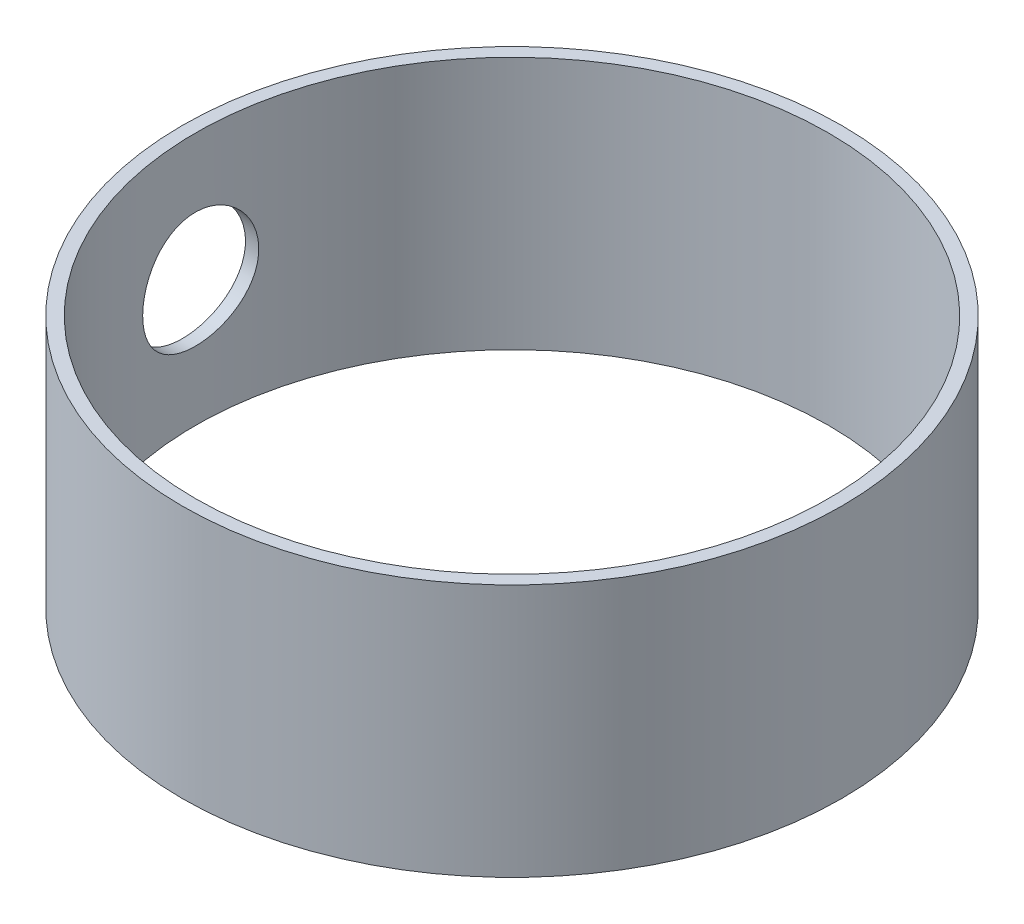
SolidWorks part; units mm, degrees
ref_plane "Front Plane" through (0, 0, 0) normal (0, 0, 1) x (1, 0, 0)
ref_plane "Top Plane" through (0, 0, 0) normal (0, 1, 0) x (1, 0, 0)
ref_plane "Right Plane" through (0, 0, 0) normal (1, 0, 0) x (0, 0, -1)
sketch "Sketch1" plane through (0, 0, 0) normal (0, 1, 0) x (1, 0, 0)
  circle A0 centre (0, 0) radius 38.1
  circle A1 centre (0, 0) radius 39.6748
  dimension "D1" = 76.2
  dimension "D2" = 79.3496
extrude "Boss-Extrude1" add sketch "Sketch1" along normal mid plane 30.48
ref_plane "Plane1" through (-39.6748, 0, 0) normal (-1, 0, 0) x (0, 0, 1)
sketch "Sketch3" plane through (-39.6748, 0, 0) normal (-1, 0, 0) x (0, 0, 1)
  circle A0 centre (0, 0) radius 6.985
  dimension "D1" = 13.97
extrude "Cut-Extrude1" cut sketch "Sketch3" against normal blind 6.35
